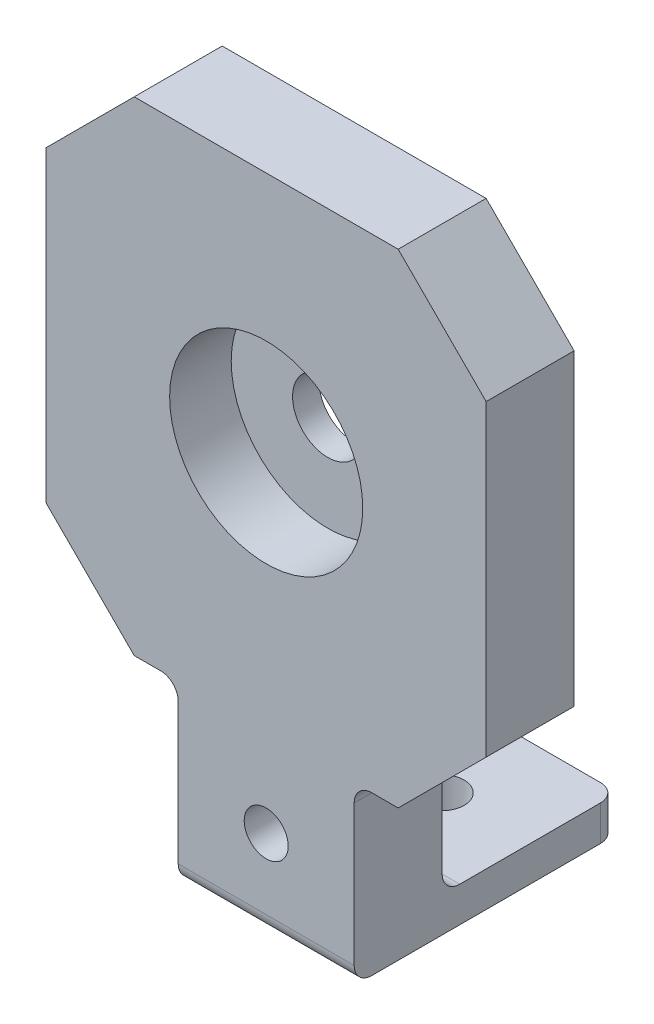
SolidWorks part; units mm, degrees
material "PLA"
ref_plane "Piano frontale" through (0, 0, 0) normal (0, 0, 1) x (1, 0, 0)
ref_plane "Piano superiore" through (0, 0, 0) normal (0, 1, 0) x (1, 0, 0)
ref_plane "Piano destro" through (0, 0, 0) normal (1, 0, 0) x (0, 0, -1)
sketch "Schizzo1" plane through (0, 0, 0) normal (0, 0, 1) x (1, 0, 0)
  line L28 (-25, 20) -> (-10, 20)
  line L37 (-25, 20) -> (-25, 75)
  line L38 (-25, 75) -> (25, 75)
  line L39 (25, 20) -> (25, 75)
  line L40 (-10, 0) -> (10, 0)
  line L41 (-10, 0) -> (-10, 20)
  line L42 (10, 0) -> (10, 20)
  line L43 (10, 20) -> (25, 20)
  circle A5 centre (0, 47.5) radius 4
  point P0 (0, 0)
  point P4 (0, 75)
  dimension "D2" = 15
  dimension "D7" = 27.5
  dimension "D6" = 8
  dimension "D1" = 15
  dimension "D4" = 50
  dimension "D3" = 55
  dimension "D5" = 20
extrude "Estrusione-Estrusione1" add sketch "Schizzo1" along normal blind 10
chamfer "Smusso1" distance 10 angle 45 4 edges at (-25, 75, 5) (-25, 20, 5) (25, 20, 5) (25, 75, 5)
sketch "Schizzo3" plane through (0, 0, 10) normal (0, 0, 1) x (1, 0, 0)
  circle A0 centre (0, 47.5) radius 10.975
  dimension "D1" = 21.95
extrude "Taglio-Estrusione1" cut sketch "Schizzo3" against normal blind 7
sketch "Schizzo4" plane through (0, 0, 0) normal (0, 0, -1) x (-1, 0, 0)
  line L0 (10, 20) -> (10, 0) construction
  line L1 (-10, 0) -> (10, 0)
  line L2 (-10, 0) -> (-10, 4)
  line L3 (-10, 4) -> (10, 4)
  line L4 (10, 0) -> (10, 4)
  dimension "D1" = 4
extrude "Estrusione-Estrusione2" add sketch "Schizzo4" along normal blind 20
fillet "Raccordo1" radius 2 6 edges at (0, 0, 10) (0, 4, 0) (-10, 20, 5) (10, 20, 5) (-10, 2, -20) (10, 2, -20)
sketch "Schizzo5" plane through (0, 4, 0) normal (0, 1, 0) x (1, 0, 0)
  line L0 (10, 0) -> (-10, 0) construction
  circle A0 centre (0, 10) radius 2.5
  dimension "D1" = 5
  dimension "D2" = 10
extrude "Taglio-Estrusione2" cut sketch "Schizzo5" against normal blind 20
sketch "Schizzo6" plane through (0, 0, 0) normal (0, 0, -1) x (-1, 0, 0)
  line L0 (-8, 0) -> (8, 0) construction
  circle A0 centre (0, 10) radius 2.5
  dimension "D1" = 5
  dimension "D2" = 10
extrude "Taglio-Estrusione3" cut sketch "Schizzo6" against normal through all
